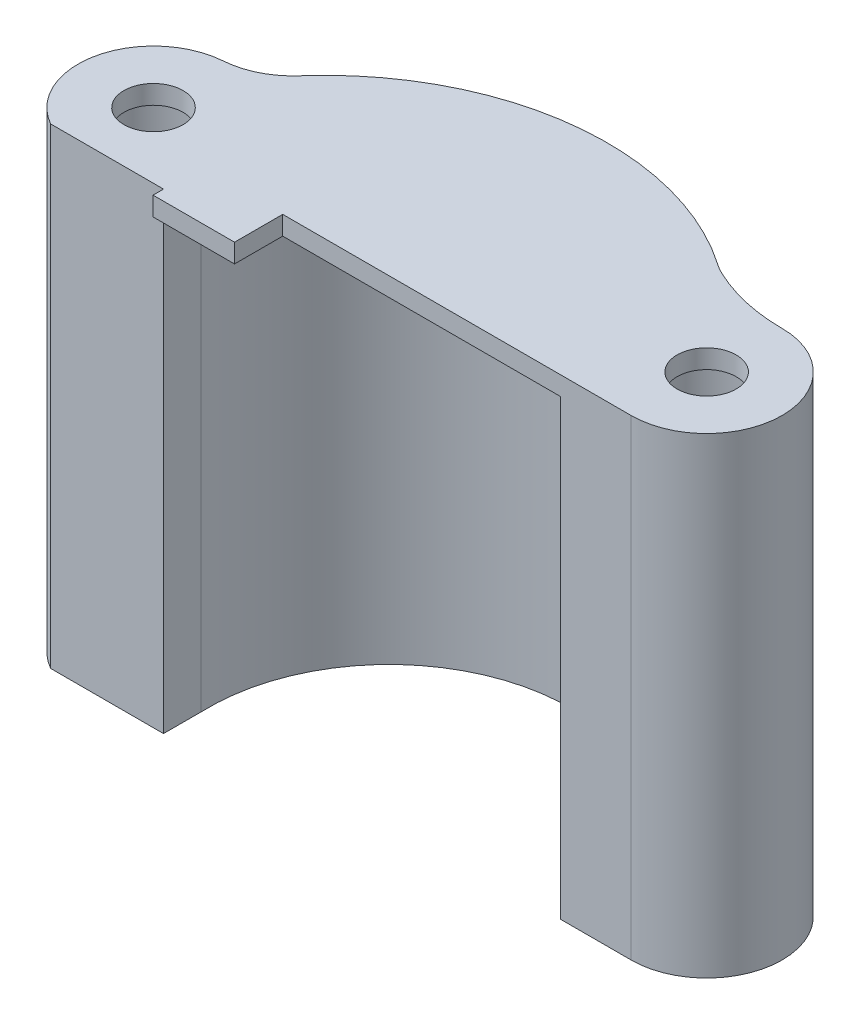
SolidWorks part; units mm, degrees
material "PLA/ABS"
ref_plane "Front Plane" through (0, 0, 0) normal (0, 0, 1) x (1, 0, 0)
ref_plane "Top Plane" through (0, 0, 0) normal (0, 1, 0) x (1, 0, 0)
ref_plane "Right Plane" through (0, 0, 0) normal (1, 0, 0) x (0, 0, -1)
other "Bounding Box"
ref_plane "Default Plane" through (-8.9266, -12.7485, 0) normal (-0.1736, 0.9848, 0) x (0.9848, 0.1736, 0)
sketch "Sketch1" plane through (0, 0, 0) normal (0, 1, 0) x (1, 0, 0)
  line B0 (-13.6378, -15.7405) -> (-16.8128, -15.7405) construction
  line B1 (16.6091, -12.5655) -> (19.7841, -12.5655) construction
  arc B2 (-13.6378, -15.7405) -> (16.6091, -12.5655) centre (1.591, -15.1567) cw
  arc B3 (-16.8128, -15.7405) -> (19.7841, -12.5655) centre (1.6704, -16.283) cw
sketch_block_instance "Cover for wepon motor-1"
sketch_block "Cover for wepon motor" parameters "D3"=15.24, "D4"=18.4912, "D1"=3.175, "D2"=3.175
sketch "Sketch2" plane through (0, 0, 0) normal (0, 1, 0) x (1, 0, 0)
  line L0 (-13.6378, -18.9155) -> (-13.6378, -15.7405)
  line L1 (16.6091, -12.5655) -> (16.6091, -15.7405)
  line L2 (-23.1387, -18.9155) -> (-13.6378, -18.9155)
  line L3 (16.6091, -15.7405) -> (22.5457, -15.7405)
  arc A1 (-13.6378, -15.7405) -> (16.6091, -12.5655) centre (1.591, -15.1567) cw
  circle A2 centre (-19.9967, -13.3973) radius 4.7625
  circle A3 centre (22.5457, -9.3905) radius 4.7625
  arc A5 (-19.9967, -7.0473) -> (-23.1387, -18.9155) centre (-19.9967, -13.3973) ccw
  arc A7 (22.5457, -15.7405) -> (22.5457, -3.0405) centre (22.5457, -9.3905) ccw
  arc A8 (-19.9967, -7.0473) -> (-17.6403, -6.7838) centre (-19.9399, 3.1125) ccw
  arc A9 (22.5457, -3.0405) -> (15.4926, -1.3102) centre (22.5457, 12.1995) cw
  arc A20 (-17.6403, -6.7838) -> (15.4926, -1.3102) centre (1.663, -20.6134) cw
  dimension "D1" = 9.525
  dimension "D2" = 15.24
  dimension "D7" = 1.5875
  dimension "D9" = 1.5875
  dimension "D10" = 10.16
  dimension "D11" = 15.24
  dimension "D4" = 3.175
extrude "Boss-Extrude1" add sketch "Sketch2" along normal blind 38.1
sketch "Sketch3" plane through (0, 38.1, 0) normal (0, 1, 0) x (-1, 0, 0)
  line L0 (13.6378, 15.7405) -> (3.5038, 15.7405)
  line L1 (3.5038, 15.7405) -> (3.5038, 12.5655)
  line L2 (3.5038, 12.5655) -> (-16.6091, 12.5655)
  line L3 (13.6378, 18.9155) -> (13.6378, 15.7405)
  line L4 (-16.6091, 12.5655) -> (-16.6091, 15.7405)
  line L5 (-16.6091, 15.7405) -> (-22.5457, 15.7405)
  line L6 (13.6378, 18.9155) -> (13.6378, 15.7405)
  line L7 (-16.6091, 12.5655) -> (-16.6091, 15.7405)
  line L8 (-16.6091, 15.7405) -> (-22.5457, 15.7405)
  line L13 (23.1387, 18.9155) -> (13.6378, 18.9155)
  line L14 (23.1387, 18.9155) -> (13.6378, 18.9155)
  circle A0 centre (-22.5457, 9.3905) radius 2.4892
  circle A2 centre (19.9967, 13.3973) radius 2.4892
  arc A9 (-15.4926, 1.3102) -> (17.6403, 6.7838) centre (-1.663, 20.6134) ccw
  arc A10 (-15.4926, 1.3102) -> (17.6403, 6.7838) centre (-1.663, 20.6134) ccw
  arc A11 (19.9967, 7.0473) -> (17.6403, 6.7838) centre (19.9399, -3.1125) ccw
  arc A12 (19.9967, 7.0473) -> (23.1387, 18.9155) centre (19.9967, 13.3973) ccw
  arc A13 (-16.6091, 12.5655) -> (13.6378, 15.7405) centre (-1.591, 15.1567) ccw
  arc A14 (-22.5457, 15.7405) -> (-22.5457, 3.0405) centre (-22.5457, 9.3905) ccw
  arc A15 (-15.4926, 1.3102) -> (-22.5457, 3.0405) centre (-22.5457, -12.1995) ccw
  arc A20 (19.9967, 7.0473) -> (17.6403, 6.7838) centre (19.9399, -3.1125) ccw
  arc A21 (19.9967, 7.0473) -> (23.1387, 18.9155) centre (19.9967, 13.3973) ccw
  arc A23 (-22.5457, 15.7405) -> (-22.5457, 3.0405) centre (-22.5457, 9.3905) ccw
  arc A24 (-15.4926, 1.3102) -> (-22.5457, 3.0405) centre (-22.5457, -12.1995) ccw
  dimension "D3" = 4.9784
  dimension "D2" = 3.175
  dimension "D4" = 20.1129
  dimension "D1" = 0
extrude "Boss-Extrude2" add sketch "Sketch3" along normal blind 1.5875
sketch "Sketch4" plane through (0, 39.6875, 0) normal (0, 1, 0) x (-1, 0, 0)
  line L0 (3.5038, 15.7405) -> (3.5038, 12.5655)
  line L1 (13.6378, 15.7405) -> (6.7798, 15.7405)
  line L2 (13.6378, 15.7405) -> (13.6378, 19.7971)
  line L3 (13.6378, 19.7971) -> (6.7798, 19.7971)
  line L4 (6.7798, 15.7405) -> (6.7798, 19.7971)
  line L5 (13.6378, 18.9155) -> (13.6378, 15.7405) construction
  line L7 (3.5038, 12.5655) -> (-16.6091, 12.5655)
  line L9 (6.7798, 15.7405) -> (-16.6091, 15.7405)
  line L10 (-16.6091, 12.5655) -> (-16.6091, 15.7405)
  line M10 (13.6378, 18.9155) -> (13.6378, 15.7405)
  line M11 (13.6378, 15.7405) -> (3.5038, 15.7405)
  line M12 (3.5038, 15.7405) -> (3.5038, 12.5655)
  line M13 (3.5038, 12.5655) -> (-16.6091, 12.5655)
  line M14 (-16.6091, 12.5655) -> (-16.6091, 15.7405)
  dimension "D1" = 6.858
  dimension "D2" = 4.0566
extrude "Boss-Extrude3" add sketch "Sketch4" against normal up to surface (1.5875 mm away) contours L9 M12 M14 M13 | L4 L3 M11 M10
fillet "Fillet2" radius 6.35 2 edges at (15.4926, 19.8438, 1.3102) (-17.6403, 19.8438, 6.7838)
